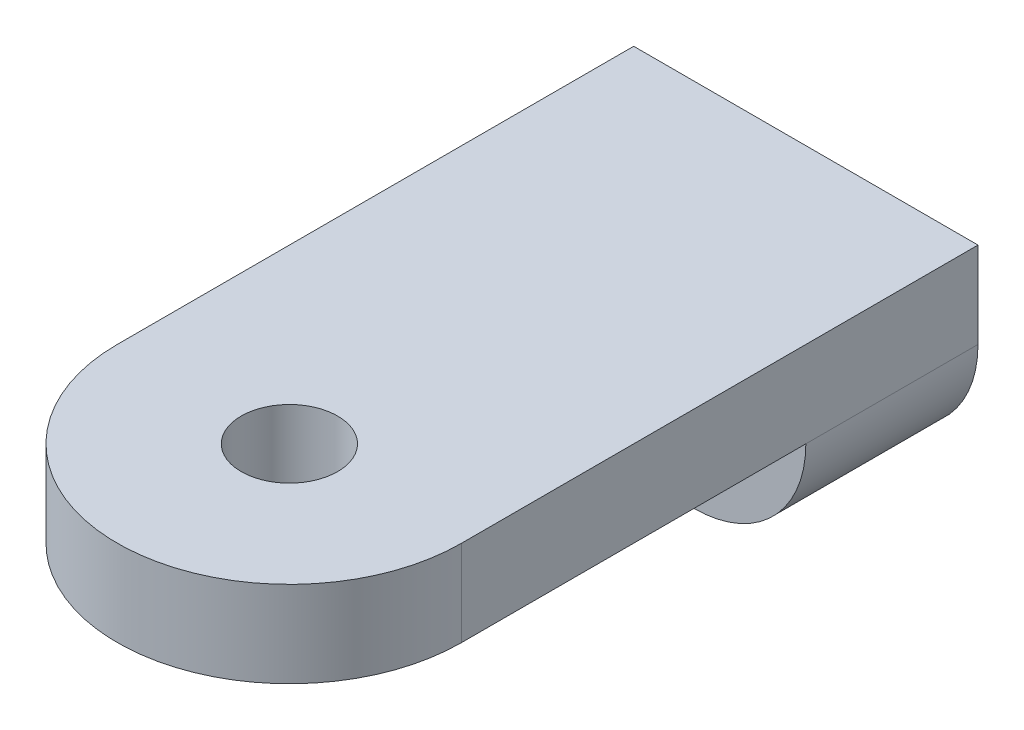
SolidWorks part; units mm, degrees
material "ABS"
ref_plane "Front" through (0, 0, 0) normal (0, 0, 1) x (1, 0, 0)
ref_plane "Top" through (0, 0, 0) normal (0, 1, 0) x (1, 0, 0)
ref_plane "Right" through (0, 0, 0) normal (1, 0, 0) x (0, 0, -1)
sketch "Sketch1" plane through (0, 0, 0) normal (0, 1, 0) x (1, 0, 0)
  line L2 (-12.7, 0) -> (-12.7, 38.1)
  line L3 (-12.7, 38.1) -> (12.7, 38.1)
  line L4 (12.7, 0) -> (12.7, 38.1)
  arc A0 (-12.7, 0) -> (12.7, 0) centre (0, 0) ccw
  circle A1 centre (0, 0) radius 3.556
  dimension "D1" = 25.4
  dimension "D2" = 7.112
  dimension "D3" = 38.1
extrude "Boss-Extrude2" add sketch "Sketch1" along normal blind 6.35
sketch "Sketch2" plane through (0, 0, 0) normal (0, -1, 0) x (1, 0, 0)
  line L0 (12.7, 0) -> (12.7, -38.1) construction
  line L1 (-12.7, -38.1) -> (12.7, -38.1)
  line L2 (-12.7, -38.1) -> (-12.7, -25.4)
  line L3 (-12.7, -25.4) -> (12.7, -25.4)
  line L4 (12.7, -38.1) -> (12.7, -25.4)
  dimension "D1" = 12.7
extrude "Boss-Extrude3" add sketch "Sketch2" along normal blind 8.255
sketch "Sketch3" plane through (0, 0, -25.4) normal (0, 0, 1) x (1, 0, 0)
  line L0 (-12.7, -8.255) -> (-12.7, 0) construction
  line L1 (-0.635, -3.175) -> (0.635, -3.175)
  line L2 (-0.635, -3.175) -> (-0.635, -6.35)
  line L3 (-0.635, -6.35) -> (0.635, -6.35)
  line L4 (0.635, -3.175) -> (0.635, -6.35)
  line L5 (-0.635, -3.175) -> (0.635, -6.35) construction
  line L6 (-0.635, -6.35) -> (0.635, -3.175) construction
  line L8 (12.7, 0) -> (-12.7, 0) construction
  point P0 (0, -4.7625)
  dimension "D1" = 1.27
  dimension "D2" = 3.175
  dimension "D3" = 12.7
  dimension "D4" = 3.175
extrude "Cut-Extrude1" cut sketch "Sketch3" against normal blind 3.175
sketch "Sketch4" plane through (0, 0, -38.1) normal (0, 0, -1) x (-1, 0, 0)
  line L3 (-12.7, -0.9525) -> (12.7, -0.9525) construction
  line L4 (-12.7, 6.35) -> (-12.7, -8.255) construction
  line L5 (12.7, 6.35) -> (12.7, -8.255) construction
  circle A0 centre (0, -0.9525) radius 6.477
  dimension "D1" = 12.954
extrude "Cut-Extrude2" cut sketch "Sketch4" against normal blind 6.604 contours A0
fillet "Fillet1" radius 8.255 2 edges at (-12.7, -8.255, -31.75) (12.7, -8.255, -31.75)
